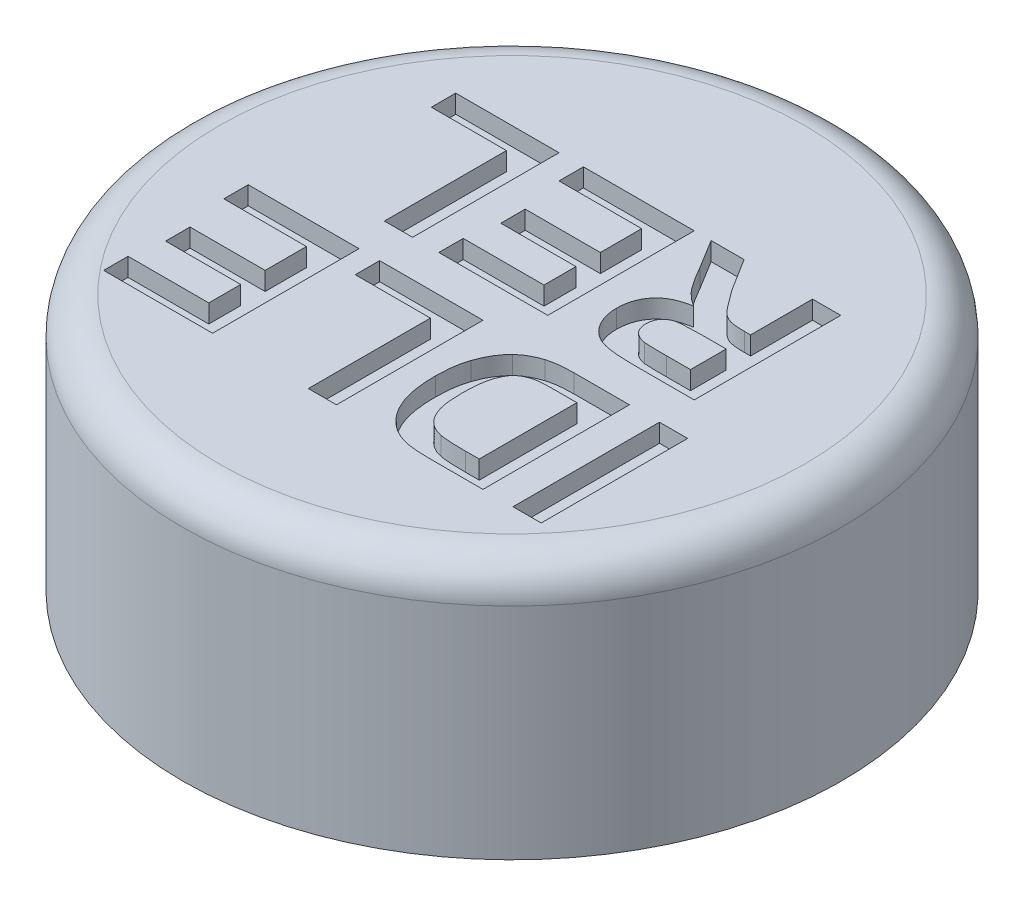
SolidWorks part; units mm, degrees
ref_plane "Спереди" through (0, 0, 0) normal (0, 0, 1) x (1, 0, 0)
ref_plane "Сверху" through (0, 0, 0) normal (0, 1, 0) x (1, 0, 0)
ref_plane "Справа" through (0, 0, 0) normal (1, 0, 0) x (0, 0, -1)
sketch "Sketch1" plane through (0, 0, 0) normal (0, 1, 0) x (1, 0, 0)
  circle A0 centre (0, 0) radius 9
  dimension "D1" = 18
extrude "Boss-Extrude1" add sketch "Sketch1" along normal blind 7
sketch "Sketch2" plane through (0, 0, 0) normal (0, -1, 0) x (1, 0, 0)
  circle A0 centre (0, 0) radius 5.2
  dimension "D1" = 10.4
extrude "Cut-Extrude1" cut sketch "Sketch2" against normal blind 4.5
sketch "Sketch3" plane through (0, 0, 0) normal (0, -1, 0) x (1, 0, 0)
  circle A0 centre (0, 0) radius 7.8
  dimension "D1" = 15.6
extrude "Cut-Extrude2" cut sketch "Sketch3" against normal blind 3
sketch "Sketch5" plane through (0, 7, 0) normal (0, 1, 0) x (1, 0, 0)
  line L0 (8.9443, -1) -> (-8.9443, -1) construction
  line L1 (9, 0) -> (-9, 0) construction
  circle A1 centre (0, 0) radius 9 construction
  text T0 "<b>IDLE</b>"
  dimension "D1" = 1
extrude "Cut-Extrude3" cut sketch "Sketch5" against normal blind 0.5
sketch "Sketch6" plane through (0, 7, 0) normal (0, 1, 0) x (1, 0, 0)
  line L0 (-9, 0) -> (9, 0) construction
  line L1 (8.0623, 4) -> (-8.0623, 4) construction
  circle A0 centre (0, 0) radius 9 construction
  text T0 "<b>REL</b>"
  dimension "D1" = 4
extrude "Cut-Extrude4" cut sketch "Sketch6" against normal blind 0.5
fillet "Fillet1" radius 1 1 edges at (0, 7, 9)
